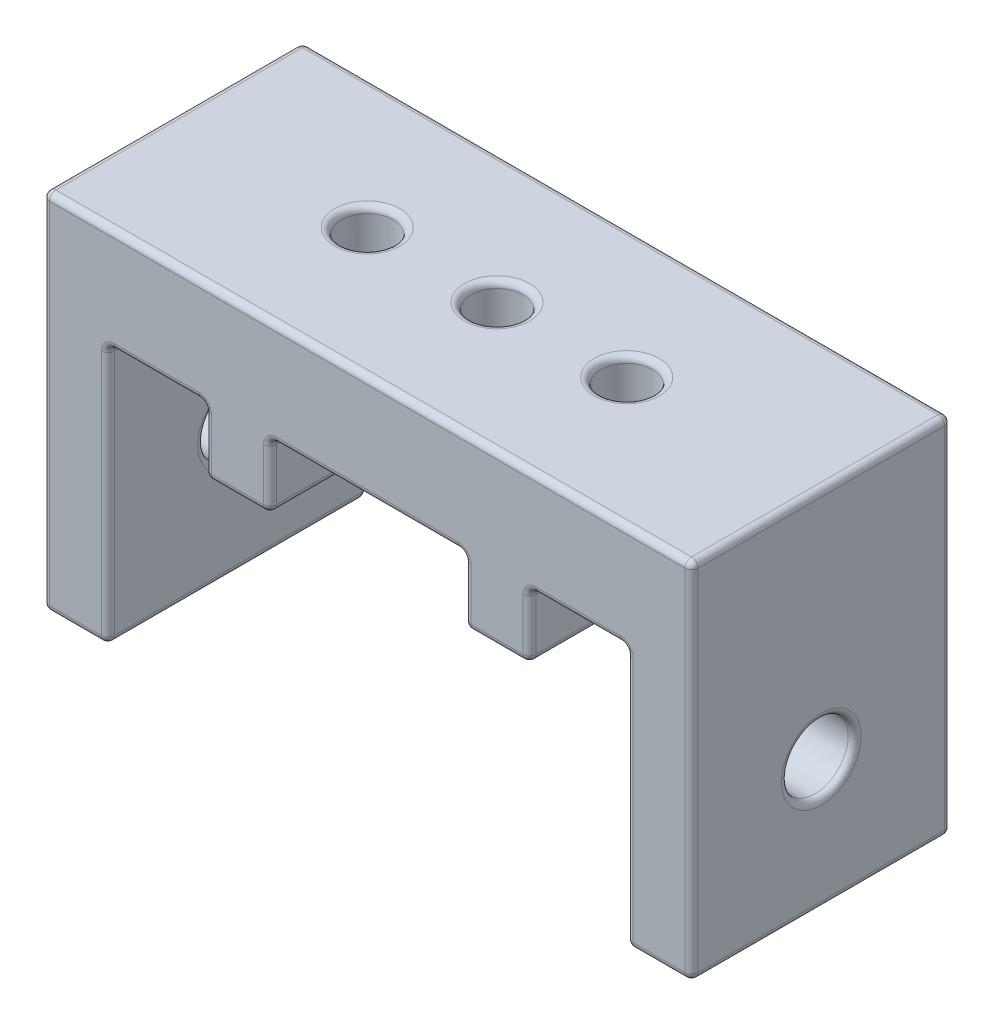
SolidWorks part; units mm, degrees
ref_plane "Front Plane" through (0, 0, 0) normal (0, 0, 1) x (1, 0, 0)
ref_plane "Top Plane" through (0, 0, 0) normal (0, 1, 0) x (1, 0, 0)
ref_plane "Right Plane" through (0, 0, 0) normal (1, 0, 0) x (0, 0, -1)
sketch "Sketch1" plane through (0, 0, 0) normal (0, 0, 1) x (1, 0, 0)
  line L0 (0, 0) -> (6.35, 0) construction
  line L1 (0, 0) -> (6.35, 0)
  line L2 (0, 0) -> (0, 35.56)
  line L3 (0, 35.56) -> (63.5, 35.56)
  line L4 (63.5, 0) -> (63.5, 35.56)
  line L5 (6.35, 0) -> (6.35, 25.4) construction
  line L6 (6.35, 25.4) -> (57.15, 25.4) construction
  line L7 (57.15, 25.4) -> (57.15, 0) construction
  line L8 (57.15, 0) -> (63.5, 0) construction
  line L9 (6.35, 0) -> (6.35, 25.4)
  line L10 (6.35, 25.4) -> (57.15, 25.4)
  line L11 (57.15, 25.4) -> (57.15, 0)
  line L12 (57.15, 0) -> (63.5, 0)
  dimension "D1" = 6.35
  dimension "D2" = 6.35
  dimension "D3" = 50.8
  dimension "D4" = 63.5
  dimension "D5" = 35.56
  dimension "D6" = 25.4
extrude "Boss-Extrude1" add sketch "Sketch1" along normal blind 25.4
sketch "Sketch2" plane through (0, 25.4, 0) normal (0, -1, 0) x (1, 0, 0)
  line L0 (0, 0) -> (19.05, 0) construction
  line L2 (19.05, 0) -> (19.05, 3.81) construction
  line L4 (22.225, 7.62) -> (15.875, 7.62)
  line L5 (22.225, 7.62) -> (22.225, 0)
  line L6 (22.225, 0) -> (15.875, 0)
  line L7 (15.875, 7.62) -> (15.875, 0)
  line L8 (22.225, 7.62) -> (15.875, 0) construction
  line L9 (22.225, 0) -> (15.875, 7.62) construction
  point P10 (-30.2331, -58.1513)
  dimension "D1" = 6.35
  dimension "D2" = 7.62
  dimension "D3" = 12.7
extrude "Boss-Extrude2" add sketch "Sketch2" along normal blind 6.35
ref_plane "Plane1" through (0, 0, 12.7) normal (0, 0, 1) x (1, 0, 0)
mirror "Mirror1" about plane through (0, 0, 12.7) normal (0, 0, 1) of "Boss-Extrude2"
hole_wizard "1/4-20 Tapped Hole1" positions "Sketch4" profile "Sketch3" tap size "1/4-20" standard "Ansi Inch" end condition through all
sketch "Sketch4" plane through (0, 35.56, 0) normal (0, 1, 0) x (-1, 0, 0)
  line L0 (-63.5, 0) -> (0, 0) construction
  line L1 (0, 25.4) -> (0, 0) construction
  point P0 (-19.05, 12.7)
  point P2 (-31.75, 0)
  dimension "D1" = 12.7
  dimension "D2" = 19.05
sketch "Sketch3" plane through (19.05, 35.56, 12.7) normal (1, 0, 0) x (0, 0, 1)
  line L0 (0, 0) -> (0, 35.56)
  line L1 (0, 35.56) -> (2.5527, 35.56)
  line L2 (2.5527, 35.56) -> (2.5527, 0)
  line L5 (2.5527, 0) -> (0, 0)
  line L11 (0, -6.35) -> (0, 107.95) construction
  dimension "Thru Tap Drill Dia." = 5.1054
  dimension "Thru Tap Drill Depth" = 35.56
cosmetic thread "Hole Thread1" parameters "D2"=6.35
hole_wizard "#97 (0.0059) Diameter Hole1" positions "Sketch6" profile "Sketch5" hole size "#97" standard "Ansi Inch"
sketch "Sketch6" plane through (6.35, 0, 0) normal (1, 0, 0) x (0, 0, -1)
  line L0 (0, 0) -> (0, 25.4) construction
  line L1 (-25.4, 25.4) -> (0, 25.4) construction
  point P0 (-12.7, 12.7)
  dimension "D1" = 12.7
  dimension "D2" = 12.7
sketch "Sketch5" plane through (6.35, 12.7, 12.7) normal (0, 1, 0) x (0, 0, -1)
  line L0 (0, 0) -> (0, 6.35)
  line L1 (0, 6.35) -> (3.2639, 6.35)
  line L2 (3.2639, 6.35) -> (3.2639, 0)
  line L5 (3.2639, 0) -> (0, 0)
  line L11 (0, -6.35) -> (0, 107.95) construction
  dimension "Thru Hole Dia." = 6.5278
  dimension "Thru Hole Depth" = 6.35
hole_wizard "#97 (0.0059) Diameter Hole2" positions "Sketch8" profile "Sketch7" hole size "#97" standard "Ansi Inch" end condition through all
sketch "Sketch8" plane through (57.15, 0, 0) normal (-1, 0, 0) x (0, 0, 1)
  line L0 (25.4, 25.4) -> (0, 25.4) construction
  line L1 (0, 25.4) -> (0, 0) construction
  point P0 (12.7, 12.7)
  dimension "D1" = 12.7
  dimension "D2" = 12.7
sketch "Sketch7" plane through (57.15, 12.7, 12.7) normal (0, 1, 0) x (0, 0, 1)
  line L0 (0, 0) -> (0, 6.35)
  line L1 (0, 6.35) -> (3.2639, 6.35)
  line L2 (3.2639, 6.35) -> (3.2639, 0)
  line L5 (3.2639, 0) -> (0, 0)
  line L11 (0, -6.35) -> (0, 107.95) construction
  dimension "Thru Hole Dia." = 6.5278
  dimension "Thru Hole Depth" = 6.35
ref_plane "Plane2" through (31.75, 0, 0) normal (1, 0, 0) x (0, 0, -1)
mirror "Mirror2" about plane through (31.75, 0, 0) normal (1, 0, 0) of "1/4-20 Tapped Hole1"
mirror "Mirror3" about plane through (31.75, 0, 0) normal (1, 0, 0) of "Boss-Extrude2", "Mirror1"
hole_wizard "1/4-20 Tapped Hole2" positions "Sketch12" profile "Sketch11" tap size "1/4-20" standard "Ansi Inch" end condition through all
sketch "Sketch12" plane through (0, 25.4, 0) normal (0, -1, 0) x (1, 0, 0)
  line L0 (22.225, 0) -> (41.275, 0) construction
  line L1 (6.35, 25.4) -> (6.35, 0) construction
  point P0 (31.75, 12.7)
  dimension "D1" = 12.7
  dimension "D2" = 25.4
sketch "Sketch11" plane through (31.75, 25.4, 12.7) normal (1, 0, 0) x (0, 0, -1)
  line L0 (0, 0) -> (0, 10.16)
  line L1 (0, 10.16) -> (2.5527, 10.16)
  line L2 (2.5527, 10.16) -> (2.5527, 0)
  line L5 (2.5527, 0) -> (0, 0)
  line L11 (0, -6.35) -> (0, 107.95) construction
  dimension "Thru Tap Drill Dia." = 5.1054
  dimension "Thru Tap Drill Depth" = 10.16
cosmetic thread "Hole Thread2" parameters "D2"=6.35
fillet "Fillet2" radius 0.635 81 edges at (47.625, 25.4, 21.59) (19.05, 25.4, 17.78) (15.875, 25.4, 3.81) (44.45, 25.4, 17.78) (47.625, 22.225, 7.62) (41.275, 22.225, 7.62) (44.45, 25.4, 7.62) (41.275, 19.05, 3.81) (44.45, 19.05, 7.62) (47.625, 19.05, 3.81) (15.875, 19.05, 21.59) (15.875, 22.225, 17.78) (15.875, 25.4, 21.59) (22.225, 22.225, 17.78) (22.225, 19.05, 21.59) (22.225, 25.4, 21.59) (6.35, 0, 12.7) (6.35, 25.4, 12.7) (6.35, 12.7, 9.4361) (3.175, 0, 0) (6.35, 12.7, 0) (11.1125, 25.4, 0) (15.875, 22.225, 0) (19.05, 19.05, 0) (22.225, 22.225, 0) (31.75, 25.4, 0) (41.275, 22.225, 0) (44.45, 19.05, 0) (47.625, 22.225, 0) (52.3875, 25.4, 0) (57.15, 12.7, 0) (60.325, 0, 0) (63.5, 17.78, 0) (31.75, 35.56, 0) (0, 17.78, 0) (31.75, 35.56, 25.4) (63.5, 17.78, 25.4) (60.325, 0, 25.4) (57.15, 12.7, 25.4) (52.3875, 25.4, 25.4) (47.625, 22.225, 25.4) (47.625, 22.225, 17.78) (44.45, 19.05, 25.4) (44.45, 19.05, 17.78) (41.275, 22.225, 17.78) (41.275, 22.225, 25.4) (31.75, 25.4, 25.4) (22.225, 22.225, 25.4) (19.05, 19.05, 17.78) (19.05, 19.05, 25.4) (15.875, 22.225, 25.4) (11.1125, 25.4, 25.4) (6.35, 12.7, 25.4) (3.175, 0, 25.4) (0, 17.78, 25.4) (15.875, 22.225, 7.62) (15.875, 19.05, 3.81) (19.05, 19.05, 7.62) (22.225, 19.05, 3.81) (22.225, 22.225, 7.62) (19.05, 25.4, 7.62) (22.225, 25.4, 3.81) (47.625, 25.4, 3.81) (41.275, 25.4, 3.81) (47.625, 19.05, 21.59) (41.275, 25.4, 21.59) (41.275, 19.05, 21.59) (57.15, 25.4, 12.7) (57.15, 12.7, 15.9639) (0, 12.7, 9.4361) (63.5, 35.56, 12.7) (0, 35.56, 12.7) (0, 0, 12.7) (57.15, 0, 12.7) (63.5, 0, 12.7) (44.45, 25.4, 15.2527) (44.45, 35.56, 15.2527) (19.05, 35.56, 15.2527) (63.5, 12.7, 15.9639) (31.75, 25.4, 10.1473) (31.75, 35.56, 10.1473)
